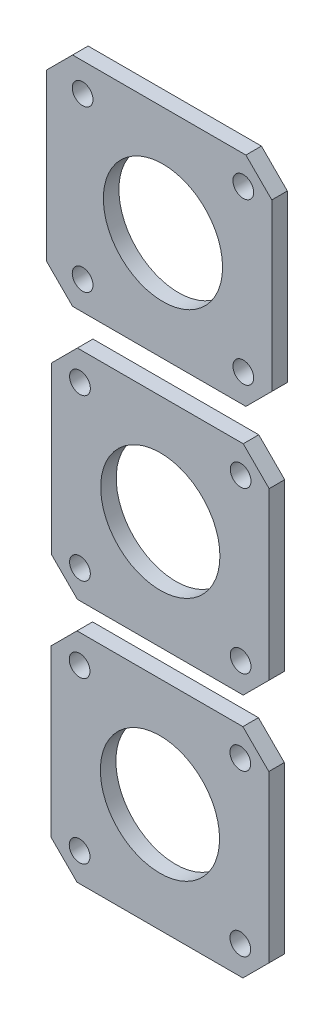
SolidWorks part; units mm, degrees
ref_plane "Piano frontale" through (0, 0, 0) normal (0, 0, 1) x (1, 0, 0)
ref_plane "Piano superiore" through (0, 0, 0) normal (0, 1, 0) x (1, 0, 0)
ref_plane "Piano destro" through (0, 0, 0) normal (1, 0, 0) x (0, 0, -1)
sketch "Schizzo1" plane through (0, 0, 0) normal (0, 0, 1) x (1, 0, 0)
  line L0 (21, 0) -> (21, 42) construction
  line L1 (5, 0) -> (37, 0)
  line L2 (0, 5) -> (0, 37)
  line L3 (5, 42) -> (37, 42)
  line L4 (42, 5) -> (42, 37)
  line L5 (5.5, 48.5694) -> (5.5, -41.0972) construction
  line L6 (-12.5669, 36.5) -> (58.9852, 36.5) construction
  line L7 (21, 21) -> (-65.3253, 21) construction
  line L8 (0, 37) -> (5, 42)
  line L9 (5, 0) -> (0, 5)
  line L10 (37, 0) -> (42, 5)
  line L11 (42, 37) -> (37, 42)
  line L12 (21.0686, 47.295) -> (21.0686, 89.295) construction
  line L13 (5.0686, 47.295) -> (37.0686, 47.295)
  line L14 (0.0686, 52.295) -> (0.0686, 84.295)
  line L15 (5.0686, 89.295) -> (37.0686, 89.295)
  line L16 (42.0686, 52.295) -> (42.0686, 84.295)
  line L17 (0.0686, 84.295) -> (5.0686, 89.295)
  line L18 (5.0686, 47.295) -> (0.0686, 52.295)
  line L19 (37.0686, 47.295) -> (42.0686, 52.295)
  line L20 (42.0686, 84.295) -> (37.0686, 89.295)
  line L21 (21.5789, 95.7897) -> (21.5789, 137.7897) construction
  line L22 (4.1417, 95.7897) -> (37.5789, 95.7897)
  line L23 (-0.8583, 100.7897) -> (-0.8583, 132.7897)
  line L24 (4.1417, 137.7897) -> (37.5789, 137.7897)
  line L25 (42.5789, 100.7897) -> (42.5789, 132.7897)
  line L26 (-0.8583, 132.7897) -> (4.1417, 137.7897)
  line L27 (4.1417, 95.7897) -> (-0.8583, 100.7897)
  line L28 (37.5789, 95.7897) -> (42.5789, 100.7897)
  line L29 (42.5789, 132.7897) -> (37.5789, 137.7897)
  circle A0 centre (21, 21) radius 11.5
  circle A1 centre (5.5, 36.5) radius 2
  circle A2 centre (5.5, 5.5) radius 2
  circle A3 centre (36.5, 5.5) radius 2
  circle A4 centre (36.5, 36.5) radius 2
  circle A5 centre (21.0686, 68.295) radius 11.5
  circle A6 centre (5.5686, 83.795) radius 2
  circle A7 centre (5.5686, 52.795) radius 2
  circle A8 centre (36.5686, 52.795) radius 2
  circle A9 centre (36.5686, 83.795) radius 2
  circle A10 centre (21.5789, 116.7897) radius 11.5
  circle A11 centre (6.0789, 132.2897) radius 2
  circle A12 centre (6.0789, 101.2897) radius 2
  circle A13 centre (37.0789, 101.2897) radius 2
  circle A14 centre (37.0789, 132.2897) radius 2
  point P0 (0, 0)
  point P1 (42, 42)
  point P2 (0, 42)
  point P3 (42, 0)
  point P13 (5.5, 36.5)
  point P15 (5.5, 5.5)
  point P17 (36.5, 5.5)
  point P18 (36.5, 36.5)
  point P35 (0.0686, 47.295)
  point P36 (42.0686, 89.295)
  point P37 (0.0686, 89.295)
  point P38 (42.0686, 47.295)
  point P43 (5.5686, 52.795)
  point P44 (36.5686, 52.795)
  point P45 (36.5686, 83.795)
  point P62 (-0.8583, 95.7897)
  point P63 (42.5789, 137.7897)
  point P64 (-0.8583, 137.7897)
  point P65 (42.5789, 95.7897)
  point P70 (6.0789, 101.2897)
  point P71 (37.0789, 101.2897)
  point P72 (37.0789, 132.2897)
  dimension "D3" = 23
  dimension "D6" = 4
  dimension "D8" = 4
  dimension "D22" = 4
  dimension "D1" = 42
  dimension "D2" = 42
  dimension "D4" = 15.5
  dimension "D5" = 15.5
  dimension "D7" = 42
  dimension "D9" = 5
  dimension "D14" = 5
  dimension "D15" = 5
  dimension "D16" = 5
  dimension "D17" = 5
  dimension "D18" = 5
  dimension "D19" = 5
  dimension "D20" = 5
  dimension "D21" = 42
  dimension "D23" = 5
  dimension "D24" = 5
  dimension "D25" = 5
  dimension "D26" = 5
  dimension "D27" = 5
  dimension "D28" = 5
  dimension "D29" = 5
  dimension "D30" = 5
extrude "Estrusione-Estrusione1" add sketch "Schizzo1" against normal blind 3
